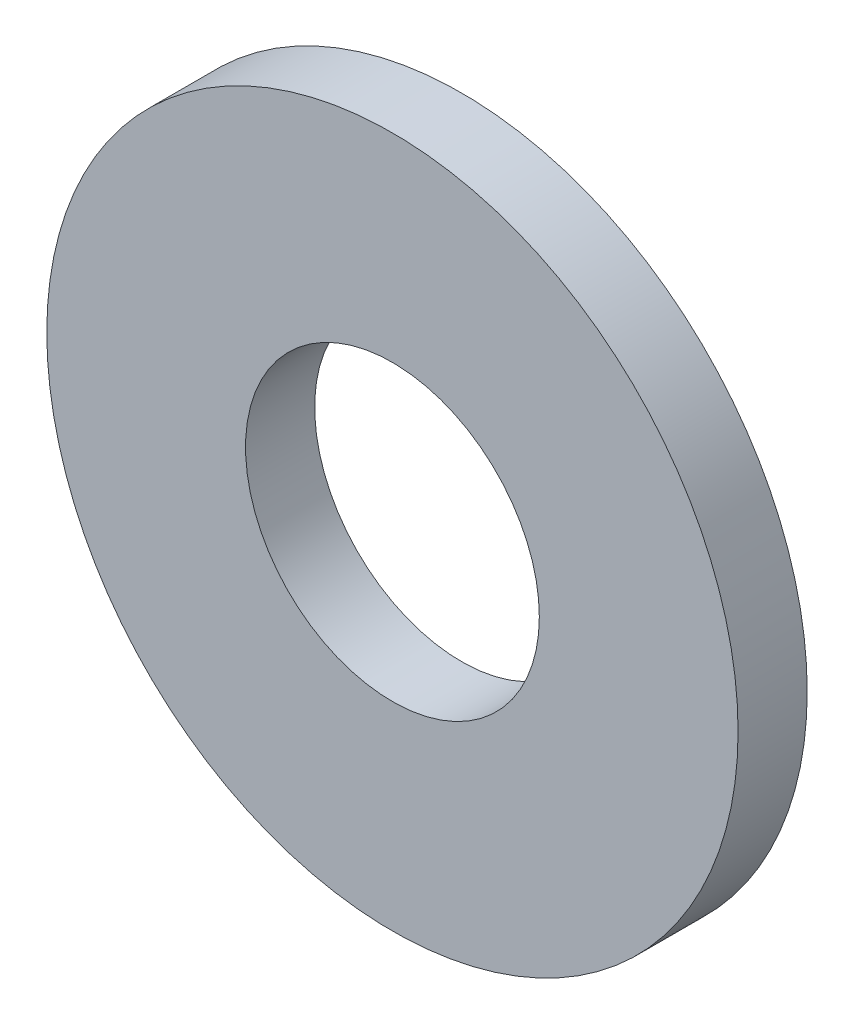
SolidWorks part; units mm, degrees
ref_plane "Front Plane" through (0, 0, 0) normal (0, 0, 1) x (1, 0, 0)
ref_plane "Top Plane" through (0, 0, 0) normal (0, 1, 0) x (1, 0, 0)
ref_plane "Right Plane" through (0, 0, 0) normal (1, 0, 0) x (0, 0, -1)
sketch "Sketch1" plane through (0, 0, 0) normal (0, 0, 1) x (1, 0, 0)
  circle A0 centre (0, 0) radius 2
  circle A1 centre (0, 0) radius 0.85
  dimension "OD" = 4
  dimension "ID1" = 1.7
extrude "Boss-Extrude1" add sketch "Sketch1" along normal blind 0.4
